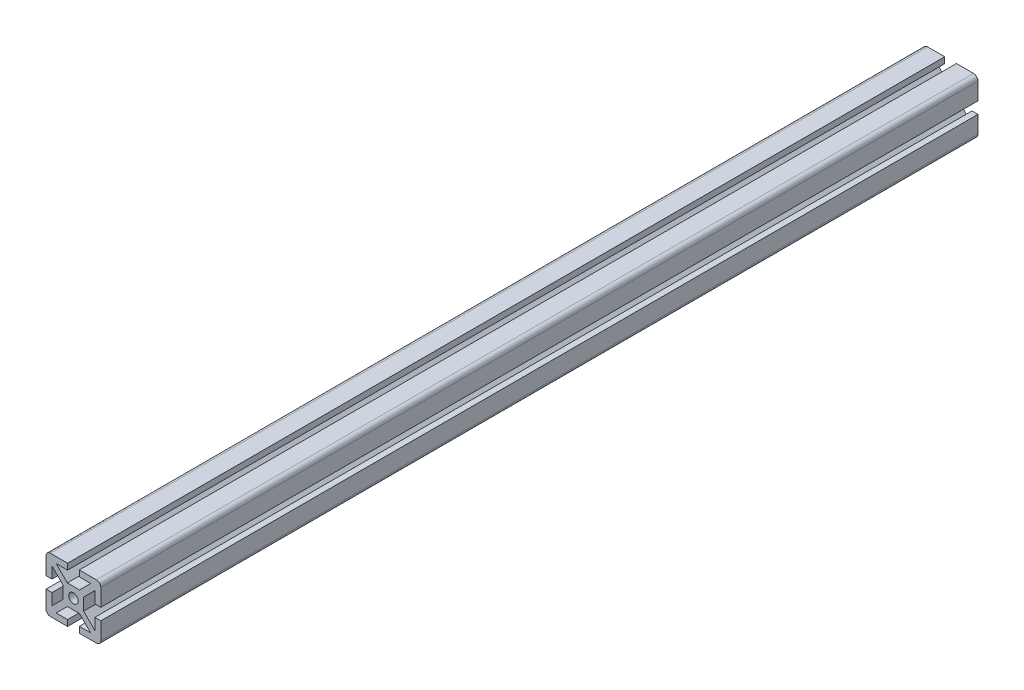
SolidWorks part; units mm, degrees
ref_plane "Front"
ref_plane "Top" through (0, 0, 0) normal (0, 1, 0) x (1, 0, 0)
ref_plane "Right" through (0, 0, 0) normal (1, 0, 0) x (0, 0, -1)
sketch "Sketch1" plane through (0, 0, 0) normal (0, 0, 1) x (1, 0, 0)
  line L0 (0, 0) -> (0, 30.3125) construction
  line L1 (0, 0) -> (-30.9262, 0) construction
  line L2 (-7.112, 0) -> (-7.112, 4.2383)
  line L3 (-7.112, 4.2383) -> (-14.8844, 12.0107)
  line L4 (-14.8844, 12.0107) -> (-14.8844, 4.064)
  line L5 (4.2383, 7.112) -> (12.0107, 14.8844)
  line L6 (-19.05, 4.064) -> (-19.05, 16.002)
  line L7 (0, 7.112) -> (-4.2383, 7.112)
  line L8 (-4.2383, 7.112) -> (-12.0107, 14.8844)
  line L9 (-12.0107, 14.8844) -> (-4.064, 14.8844)
  line L10 (4.064, 19.05) -> (16.002, 19.05)
  line L11 (-4.064, 19.05) -> (-16.002, 19.05)
  line L12 (19.05, 4.064) -> (19.05, 16.002)
  line L13 (12.0107, 14.8844) -> (4.064, 14.8844)
  line L14 (14.8844, 12.0107) -> (14.8844, 4.064)
  line L15 (7.112, 4.2383) -> (14.8844, 12.0107)
  line L16 (7.112, 0) -> (7.112, 4.2383)
  line L17 (7.112, 0) -> (7.112, -4.2383)
  line L18 (4.2383, -7.112) -> (0, -7.112)
  line L19 (7.112, -4.2383) -> (14.8844, -12.0107)
  line L20 (14.8844, -12.0107) -> (14.8844, -4.064)
  line L21 (4.2383, -7.112) -> (12.0107, -14.8844)
  line L22 (19.05, -4.064) -> (19.05, -16.002)
  line L23 (-4.064, -19.05) -> (-16.002, -19.05)
  line L24 (4.064, -19.05) -> (16.002, -19.05)
  line L25 (12.0107, -14.8844) -> (4.064, -14.8844)
  line L26 (-4.2383, -7.112) -> (-12.0107, -14.8844)
  line L27 (0, -7.112) -> (-4.2383, -7.112)
  line L28 (-19.05, -4.064) -> (-19.05, -16.002)
  line L29 (-12.0107, -14.8844) -> (-4.064, -14.8844)
  line L30 (-14.8844, -12.0107) -> (-14.8844, -4.064)
  line L31 (-7.112, -4.2383) -> (-14.8844, -12.0107)
  line L32 (-7.112, 0) -> (-7.112, -4.2383)
  line L33 (0, 7.112) -> (4.2383, 7.112)
  line L34 (-4.064, 19.05) -> (-4.064, 14.8844)
  line L35 (4.064, 19.05) -> (4.064, 14.8844)
  line L36 (-14.8844, 4.064) -> (-19.05, 4.064)
  line L37 (14.8844, 4.064) -> (19.05, 4.064)
  line L38 (-4.064, -19.05) -> (-4.064, -14.8844)
  line L39 (-14.8844, -4.064) -> (-19.05, -4.064)
  line L40 (14.8844, -4.064) -> (19.05, -4.064)
  line L41 (4.064, -19.05) -> (4.064, -14.8844)
  arc A0 (-16.002, 19.05) -> (-19.05, 16.002) centre (-16.002, 16.002) ccw
  arc A6 (16.002, 19.05) -> (19.05, 16.002) centre (16.002, 16.002) cw
  arc A13 (16.002, -19.05) -> (19.05, -16.002) centre (16.002, -16.002) ccw
  arc A19 (-16.002, -19.05) -> (-19.05, -16.002) centre (-16.002, -16.002) cw
  circle A20 centre (0, 0) radius 3.2639
  dimension "D2" = 3.048
  dimension "D5" = 4.064
  dimension "D6" = 14.986
  dimension "D15" = 6.5278
  dimension "D3" = 11.938
  dimension "D1" = 45
  dimension "D4" = 11.938
  dimension "D8" = 7.7724
  dimension "D9" = 19.05
  dimension "D10" = 19.05
  dimension "D11" = 7.7724
extrude "FinalCut" add sketch "Sketch1" against normal blind 609.6
ref_plane "A" through (0, 0, 0) normal (0, 0, 1) x (1, 0, 0)
ref_plane "B" through (0, 0, -609.6) normal (0, 0, -1) x (-1, 0, 0)
ref_plane "Y+" through (0, 19.05, 0) normal (0, 1, 0) x (-1, 0, 0)
ref_plane "X+" through (19.05, 0, 0) normal (1, 0, 0) x (0, 0, -1)
ref_plane "Y-" through (0, -19.05, 0) normal (0, -1, 0) x (1, 0, 0)
ref_plane "X-" through (-19.05, 0, 0) normal (-1, 0, 0) x (0, 0, 1)
ref_plane "SLOT-1-3-" through (0, 0, 0) normal (1, 0, 0) x (0, 0, -1)
ref_plane "SLOT-2-4-" through (0, 0, 0) normal (0, 1, 0) x (-1, 0, 0)
sketch "Sketch38" plane through (0, 0, -609.6) normal (0, 0, -1) x (-1, 0, 0)
  point P0 (0, 0)
sketch "Sketch3" plane through (0, 19.05, 0) normal (0, 1, 0) x (-1, 0, 0)
  line L0 (4.064, 0) -> (16.002, 0) construction
  circle A0 centre (0, -21.717) radius 10.3124
  dimension "D1" = 20.6248
  dimension "D2" = 21.717
extrude "AFA1" [suppressed] cut sketch "Sketch3" against normal blind 16.51
sketch "Sketch5" plane through (19.05, 0, 0) normal (1, 0, 0) x (0, 0, -1)
  line L0 (0, 4.064) -> (0, 16.002) construction
  circle A0 centre (21.717, 0) radius 10.3124
  dimension "D1" = 20.6248
  dimension "D2" = 21.717
extrude "AFA2" [suppressed] cut sketch "Sketch5" against normal blind 16.51
sketch "Sketch6" plane through (0, -19.05, 0) normal (0, -1, 0) x (1, 0, 0)
  circle A0 centre (0, -21.717) radius 10.3124
  dimension "D1" = 21.717
  dimension "D2" = 20.6248
extrude "AFA3" [suppressed] cut sketch "Sketch6" against normal blind 16.51
sketch "Sketch8" plane through (-19.05, 0, 0) normal (-1, 0, 0) x (0, 0, 1)
  circle A0 centre (-21.717, 0) radius 10.3124
  dimension "D2" = 20.6248
  dimension "D1" = 21.717
extrude "AFA4" [suppressed] cut sketch "Sketch8" against normal blind 16.51
sketch "Sketch9" plane through (0, 19.05, 0) normal (0, 1, 0) x (-1, 0, 0)
  line L0 (-16.002, -609.6) -> (-4.064, -609.6) construction
  circle A0 centre (0, -587.883) radius 10.3124
  dimension "D2" = 20.6248
  dimension "D1" = 21.717
extrude "AFB1" [suppressed] cut sketch "Sketch9" against normal blind 16.51
sketch "Sketch12" plane through (19.05, 0, 0) normal (1, 0, 0) x (0, 0, -1)
  line L0 (609.6, 4.064) -> (609.6, 16.002) construction
  circle A0 centre (587.883, 0) radius 10.3124
  dimension "D2" = 20.6248
  dimension "D1" = 21.717
extrude "AFB2" [suppressed] cut sketch "Sketch12" against normal blind 16.51
sketch "Sketch13" plane through (0, -19.05, 0) normal (0, -1, 0) x (1, 0, 0)
  line L0 (-16.002, -609.6) -> (-4.064, -609.6) construction
  circle A0 centre (0, -587.883) radius 10.3124
  point P2 (-10.033, -609.6)
  dimension "D3" = 20.6248
  dimension "D1" = 0
  dimension "D2" = 21.717
extrude "AFB3" [suppressed] cut sketch "Sketch13" against normal blind 16.51
sketch "Sketch14" plane through (-19.05, 0, 0) normal (-1, 0, 0) x (0, 0, 1)
  line L0 (-609.6, 16.002) -> (-609.6, 4.064) construction
  circle A0 centre (-587.883, 0) radius 10.3124
  dimension "D2" = 20.6248
  dimension "D1" = 21.717
extrude "AFB4" [suppressed] cut sketch "Sketch14" against normal blind 16.51
sketch "Sketch25" plane through (0, 19.05, 0) normal (0, 1, 0) x (-1, 0, 0)
  circle A0 centre (0, -18.3134) radius 10.3124
  dimension "D1" = 20.6248
  dimension "D2" = 18.3134
extrude "BFA1" [suppressed] cut sketch "Sketch25" against normal blind 16.51
sketch "Sketch27" plane through (19.05, 0, 0) normal (1, 0, 0) x (0, 0, -1)
  line L0 (0, 4.064) -> (0, 16.002) construction
  circle A0 centre (18.3134, 0) radius 10.3124
  dimension "D1" = 20.6248
  dimension "D2" = 18.3134
extrude "BFA2" [suppressed] cut sketch "Sketch27" against normal blind 16.51
sketch "Sketch24" plane through (0, -19.05, 0) normal (0, -1, 0) x (1, 0, 0)
  circle A0 centre (0, -18.3134) radius 10.3124
  dimension "D1" = 18.3134
  dimension "D2" = 20.6248
extrude "BFA3" [suppressed] cut sketch "Sketch24" against normal blind 16.51
sketch "Sketch23" plane through (-19.05, 0, 0) normal (-1, 0, 0) x (0, 0, 1)
  circle A0 centre (-18.3134, 0) radius 10.3124
  dimension "D1" = 18.3134
  dimension "D2" = 20.6248
extrude "BFA4" [suppressed] cut sketch "Sketch23" against normal blind 16.51
sketch "Sketch15" plane through (0, 19.05, 0) normal (0, 1, 0) x (-1, 0, 0)
  line L0 (-20.955, -609.6) -> (20.955, -609.6) construction
  circle A0 centre (0, -591.2866) radius 10.3124
  dimension "D2" = 20.6248
  dimension "D1" = 18.3134
extrude "BFB1" [suppressed] cut sketch "Sketch15" against normal blind 16.51
sketch "Sketch17" plane through (19.05, 0, 0) normal (1, 0, 0) x (0, 0, -1)
  line L0 (609.6, -20.955) -> (609.6, 20.955) construction
  circle A0 centre (591.2866, 0) radius 10.3124
  dimension "D2" = 20.6248
  dimension "D1" = 18.3134
extrude "BFB2" [suppressed] cut sketch "Sketch17" against normal blind 16.51
sketch "Sketch18" plane through (0, -19.05, 0) normal (0, -1, 0) x (1, 0, 0)
  line L0 (-20.955, -609.6) -> (20.955, -609.6) construction
  circle A0 centre (0, -591.2866) radius 10.3124
  dimension "D2" = 20.6248
  dimension "D1" = 18.3134
extrude "BFB3" [suppressed] cut sketch "Sketch18" against normal blind 16.51
sketch "Sketch19" plane through (-19.05, 0, 0) normal (-1, 0, 0) x (0, 0, 1)
  line L0 (-609.6, 20.955) -> (-609.6, -20.955) construction
  circle A0 centre (-591.2866, 0) radius 10.3124
  dimension "D2" = 20.6248
  dimension "D1" = 18.3134
extrude "BFB4" [suppressed] cut sketch "Sketch19" against normal blind 16.51
sketch "Sketch28" plane through (0, 0, 0) normal (0, 0, 1) x (1, 0, 0)
  circle A0 centre (0, 0) radius 3.81
  dimension "D1" = 7.62
extrude "TPA660015" [suppressed] cut sketch "Sketch28" against normal blind 25.4
sketch "Sketch29" plane through (0, 0, -609.6) normal (0, 0, -1) x (-1, 0, 0)
  circle A0 centre (0, 0) radius 3.81
  dimension "D1" = 7.62
extrude "TPB660015" [suppressed] cut sketch "Sketch29" against normal blind 25.4
sketch "Sketch30" plane through (0, 0, 0) normal (0, 0, 1) x (1, 0, 0)
  circle A0 centre (0, 0) radius 3.937
  dimension "D1" = 7.874
extrude "TPA660034" [suppressed] cut sketch "Sketch30" against normal blind 24.13
sketch "Sketch31" plane through (0, 0, -609.6) normal (0, 0, -1) x (-1, 0, 0)
  circle A0 centre (0, 0) radius 3.937
  dimension "D1" = 7.874
extrude "TPB660034" [suppressed] cut sketch "Sketch31" against normal blind 24.13
sketch "Sketch32" plane through (0, 0, 0) normal (0, 0, 1) x (1, 0, 0)
  circle A0 centre (0, 0) radius 4.064
  dimension "D1" = 8.128
extrude "TPA660033" [suppressed] cut sketch "Sketch32" against normal blind 22.86
sketch "Sketch33" plane through (0, 0, -609.6) normal (0, 0, -1) x (-1, 0, 0)
  circle A0 centre (0, 0) radius 4.064
  dimension "D1" = 8.128
extrude "TPB660033" [suppressed] cut sketch "Sketch33" against normal blind 22.86
sketch "Sketch34" plane through (0, 0, 0) normal (0, 0, 1) x (1, 0, 0)
  circle A0 centre (0, 0) radius 4.7625
  dimension "D1" = 9.525
extrude "TPA660009" [suppressed] cut sketch "Sketch34" against normal blind 21.59
sketch "Sketch35" plane through (0, 0, -609.6) normal (0, 0, -1) x (-1, 0, 0)
  circle A0 centre (0, 0) radius 4.7625
  dimension "D1" = 9.525
extrude "TPB660009" [suppressed] cut sketch "Sketch35" against normal blind 21.59
sketch "Sketch36" plane through (0, 0, 0) normal (0, 0, 1) x (1, 0, 0)
  circle A0 centre (0, 0) radius 5.5626
  dimension "D1" = 11.1252
extrude "TPA660030" [suppressed] cut sketch "Sketch36" against normal blind 20.32
sketch "Sketch37" plane through (0, 0, -609.6) normal (0, 0, -1) x (-1, 0, 0)
  circle A0 centre (0, 0) radius 5.5626
  dimension "D1" = 11.1252
extrude "TPB660030" [suppressed] cut sketch "Sketch37" against normal blind 20.32
sketch "Sketch39" plane through (0, 0, 0) normal (1, 0, 0) x (0, 0, -1)
  line L0 (0, 19.05) -> (38.1, -19.05)
  line L1 (609.6, 19.05) -> (0, 19.05) construction
  line L2 (609.6, -19.05) -> (0, -19.05) construction
  dimension "D1" = 45
extrude "MITA1" [suppressed] cut sketch "Sketch39" against normal through all and the other way through all flip side to cut
ref_plane "AMITA1" [suppressed] through (0, 9.525, -9.525) normal (0, 0.7071, -0.7071) x (-1, 0, 0)
ref_plane "AMITOFFA1" [suppressed] through (0, 14.0151, -14.0151) normal (0, 0.7071, -0.7071) x (-1, 0, 0)
sketch "Sketch43" [suppressed] plane through (0, 14.0151, -14.0151) normal (0, 0.7071, -0.7071) x (-1, 0, 0)
  line L0 (4.064, 13.4704) -> (16.002, 13.4704) construction
  circle A0 centre (0, -15.1046) radius 9.525
  dimension "D2" = 19.05
  dimension "D1" = 28.575
extrude "MITCBA1" [suppressed] cut sketch "Sketch43" along normal through all
sketch "Sketch44" [suppressed] plane through (0, 14.0151, -14.0151) normal (0, 0.7071, -0.7071) x (-1, 0, 0)
  line L0 (4.064, 13.4704) -> (16.002, 13.4704) construction
  circle A0 centre (0, -15.1046) radius 4.1656
  dimension "D1" = 8.3312
  dimension "D2" = 28.575
extrude "MITDRA1" [suppressed] cut sketch "Sketch44" against normal through all
sketch "Sketch45" [suppressed] plane through (0, 14.0151, -14.0151) normal (0, 0.7071, -0.7071) x (-1, 0, 0)
  line L0 (-9.525, 13.4704) -> (-9.525, -4.0048)
  line L1 (9.525, -4.0048) -> (9.525, 13.4704)
  line L2 (9.525, 13.4704) -> (-9.525, 13.4704)
  line L3 (4.064, 13.4704) -> (16.002, 13.4704) construction
  arc A0 (-9.525, -4.0048) -> (9.525, -4.0048) centre (0, -4.0048) ccw
  dimension "D1" = 17.4752
  dimension "D2" = 9.525
extrude "MITEBA1" [suppressed] cut sketch "Sketch45" along normal through all
sketch "Sketch46" [suppressed] plane through (0, 14.0151, -14.0151) normal (0, 0.7071, -0.7071) x (-1, 0, 0)
  line L0 (-4.1656, 13.4704) -> (-4.1656, -4.0048)
  line L1 (4.1656, -4.0048) -> (4.1656, 13.4704)
  line L2 (4.1656, 13.4704) -> (-4.1656, 13.4704)
  line L3 (4.064, 13.4704) -> (16.002, 13.4704) construction
  arc A0 (-4.1656, -4.0048) -> (4.1656, -4.0048) centre (0, -4.0048) ccw
  dimension "D1" = 4.1656
  dimension "D2" = 17.4752
extrude "MITEDA1" [suppressed] cut sketch "Sketch46" against normal through all
sketch "Sketch40" plane through (0, 0, 0) normal (1, 0, 0) x (0, 0, -1)
  line L0 (609.6, 19.05) -> (571.5, -19.05)
  line L1 (609.6, 19.05) -> (0, 19.05) construction
  line L2 (609.6, -19.05) -> (0, -19.05) construction
  dimension "D1" = 45
extrude "MITB1" [suppressed] cut sketch "Sketch40" against normal through all and the other way through all
ref_plane "AMITB1" [suppressed] through (0, -41.275, -41.275) normal (0, 0.7071, 0.7071) x (1, 0, 0)
ref_plane "AMITOFFB1" [suppressed] through (0, -36.7849, -36.7849) normal (0, 0.7071, 0.7071) x (1, 0, 0)
sketch "Sketch47" [suppressed] plane through (0, -36.7849, -36.7849) normal (0, 0.7071, 0.7071) x (1, 0, 0)
  line L0 (16.002, 85.3124) -> (4.064, 85.3124) construction
  circle A0 centre (0, 56.7374) radius 9.525
  dimension "D1" = 28.575
  dimension "D2" = 19.05
extrude "MITCBB1" [suppressed] cut sketch "Sketch47" along normal through all
sketch "Sketch48" [suppressed] plane through (0, -36.7849, -36.7849) normal (0, 0.7071, 0.7071) x (1, 0, 0)
  line L0 (16.002, 85.3124) -> (4.064, 85.3124) construction
  circle A0 centre (0, 56.7374) radius 4.1656
  dimension "D1" = 28.575
  dimension "D2" = 8.3312
extrude "MITDRB1" [suppressed] cut sketch "Sketch48" against normal through all
sketch "Sketch49" [suppressed] plane through (0, -36.7849, -36.7849) normal (0, 0.7071, 0.7071) x (1, 0, 0)
  line L0 (-9.525, 67.8372) -> (-9.525, 85.3124)
  line L1 (-9.525, 85.3124) -> (9.525, 85.3124)
  line L2 (9.525, 85.3124) -> (9.525, 67.8372)
  line L3 (16.002, 85.3124) -> (4.064, 85.3124) construction
  arc A0 (9.525, 67.8372) -> (-9.525, 67.8372) centre (0, 67.8372) cw
  dimension "D2" = 9.525
  dimension "D1" = 17.4752
extrude "MITEBB1" [suppressed] cut sketch "Sketch49" along normal through all
sketch "Sketch50" [suppressed] plane through (0, -36.7849, -36.7849) normal (0, 0.7071, 0.7071) x (1, 0, 0)
  line L0 (-4.1656, 85.3124) -> (-4.1656, 67.8372)
  line L1 (4.1656, 67.8372) -> (4.1656, 85.3124)
  line L2 (4.1656, 85.3124) -> (-4.1656, 85.3124)
  line L3 (16.002, 85.3124) -> (4.064, 85.3124) construction
  arc A0 (-4.1656, 67.8372) -> (4.1656, 67.8372) centre (0, 67.8372) ccw
  dimension "D2" = 4.1656
  dimension "D1" = 17.4752
extrude "MITEDB1" [suppressed] cut sketch "Sketch50" against normal through all
sketch "Sketch41" plane through (0, 0, 0) normal (1, 0, 0) x (0, 0, -1)
  line L0 (0, -19.05) -> (38.1, 19.05)
  line L1 (609.6, -19.05) -> (0, -19.05) construction
  line L2 (609.6, 19.05) -> (0, 19.05) construction
  dimension "D1" = 45
extrude "MITA3" [suppressed] cut sketch "Sketch41" against normal through all and the other way through all
ref_plane "AMITA3" [suppressed] through (0, -9.525, -9.525) normal (0, -0.7071, -0.7071) x (-1, 0, 0)
ref_plane "AMITOFFA3" [suppressed] through (0, -14.0151, -14.0151) normal (0, -0.7071, -0.7071) x (-1, 0, 0)
sketch "Sketch51" [suppressed] plane through (0, -14.0151, -14.0151) normal (0, -0.7071, -0.7071) x (-1, 0, 0)
  line L0 (16.002, -13.4704) -> (4.064, -13.4704) construction
  circle A0 centre (0, 15.1046) radius 9.525
  dimension "D1" = 19.05
  dimension "D2" = 28.575
extrude "MITCBA3" [suppressed] cut sketch "Sketch51" along normal through all
sketch "Sketch52" [suppressed] plane through (0, -14.0151, -14.0151) normal (0, -0.7071, -0.7071) x (-1, 0, 0)
  line L0 (16.002, -13.4704) -> (4.064, -13.4704) construction
  circle A0 centre (0, 15.1046) radius 4.1656
  dimension "D1" = 28.575
  dimension "D2" = 8.3312
extrude "MITDRA3" [suppressed] cut sketch "Sketch52" against normal through all
sketch "Sketch53" [suppressed] plane through (0, -14.0151, -14.0151) normal (0, -0.7071, -0.7071) x (-1, 0, 0)
  line L0 (-9.525, -13.4704) -> (-9.525, 4.0048)
  line L1 (9.525, 4.0048) -> (9.525, -13.4704)
  line L2 (9.525, -13.4704) -> (-9.525, -13.4704)
  line L3 (16.002, -13.4704) -> (4.064, -13.4704) construction
  arc A0 (-9.525, 4.0048) -> (9.525, 4.0048) centre (0, 4.0048) cw
  dimension "D1" = 9.525
  dimension "D2" = 17.4752
extrude "MITEBA3" [suppressed] cut sketch "Sketch53" along normal through all
sketch "Sketch54" [suppressed] plane through (0, -14.0151, -14.0151) normal (0, -0.7071, -0.7071) x (-1, 0, 0)
  line L0 (-4.1656, -13.4704) -> (-4.1656, 4.0048)
  line L1 (4.1656, 4.0048) -> (4.1656, -13.4704)
  line L2 (4.1656, -13.4704) -> (-4.1656, -13.4704)
  line L3 (16.002, -13.4704) -> (4.064, -13.4704) construction
  arc A0 (-4.1656, 4.0048) -> (4.1656, 4.0048) centre (0, 4.0048) cw
  dimension "D1" = 4.1656
  dimension "D2" = 17.4752
extrude "MITEDA3" [suppressed] cut sketch "Sketch54" against normal through all
sketch "Sketch42" plane through (0, 0, 0) normal (1, 0, 0) x (0, 0, -1)
  line L0 (609.6, -19.05) -> (571.5, 19.05)
  line L1 (609.6, -19.05) -> (0, -19.05) construction
  line L2 (609.6, 19.05) -> (0, 19.05) construction
  dimension "D1" = 45
extrude "MITB3" [suppressed] cut sketch "Sketch42" against normal through all and the other way through all flip side to cut
ref_plane "AMITB3" [suppressed] through (0, 41.275, -41.275) normal (0, -0.7071, 0.7071) x (1, 0, 0)
ref_plane "AMITOFFB3" [suppressed] through (0, 36.7849, -36.7849) normal (0, -0.7071, 0.7071) x (1, 0, 0)
sketch "Sketch55" [suppressed] plane through (0, 36.7849, -36.7849) normal (0, -0.7071, 0.7071) x (1, 0, 0)
  line L0 (4.064, -85.3124) -> (16.002, -85.3124) construction
  circle A0 centre (0, -56.7374) radius 9.525
  dimension "D1" = 19.05
  dimension "D2" = 28.575
extrude "MITCBB3" [suppressed] cut sketch "Sketch55" along normal through all
sketch "Sketch56" [suppressed] plane through (0, 36.7849, -36.7849) normal (0, -0.7071, 0.7071) x (1, 0, 0)
  line L0 (4.064, -85.3124) -> (16.002, -85.3124) construction
  circle A0 centre (0, -56.7374) radius 4.1656
  dimension "D1" = 28.575
  dimension "D2" = 8.3312
extrude "MITDRB3" [suppressed] cut sketch "Sketch56" against normal through all
sketch "Sketch57" [suppressed] plane through (0, 36.7849, -36.7849) normal (0, -0.7071, 0.7071) x (1, 0, 0)
  line L0 (-9.525, -85.3124) -> (-9.525, -67.8372)
  line L1 (9.525, -67.8372) -> (9.525, -85.3124)
  line L2 (9.525, -85.3124) -> (-9.525, -85.3124)
  line L3 (4.064, -85.3124) -> (16.002, -85.3124) construction
  arc A0 (-9.525, -67.8372) -> (9.525, -67.8372) centre (0, -67.8372) cw
  dimension "D1" = 17.4752
  dimension "D2" = 9.525
extrude "MITEBB3" [suppressed] cut sketch "Sketch57" along normal through all
sketch "Sketch58" [suppressed] plane through (0, 36.7849, -36.7849) normal (0, -0.7071, 0.7071) x (1, 0, 0)
  line L0 (-4.1656, -85.3124) -> (-4.1656, -67.8372)
  line L1 (4.1656, -67.8372) -> (4.1656, -85.3124)
  line L2 (4.1656, -85.3124) -> (-4.1656, -85.3124)
  line L3 (4.064, -85.3124) -> (16.002, -85.3124) construction
  arc A0 (-4.1656, -67.8372) -> (4.1656, -67.8372) centre (0, -67.8372) cw
  dimension "D1" = 17.4752
  dimension "D2" = 4.1656
extrude "MITEDB3" [suppressed] cut sketch "Sketch58" against normal through all
